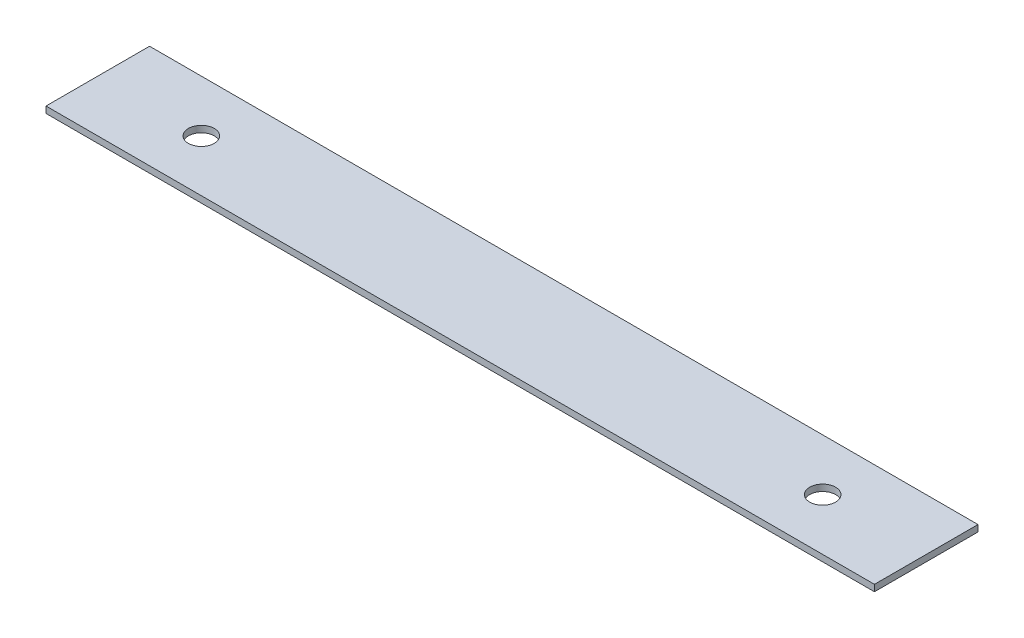
SolidWorks part; units mm, degrees
ref_plane "Front Plane" through (0, 0, 0) normal (0, 0, 1) x (1, 0, 0)
ref_plane "Top Plane" through (0, 0, 0) normal (0, 1, 0) x (1, 0, 0)
ref_plane "Right Plane" through (0, 0, 0) normal (1, 0, 0) x (0, 0, -1)
sketch "Sketch1" plane through (0, 0, 0) normal (0, 1, 0) x (1, 0, 0)
  line L0 (-203.2, 0) -> (203.2, 0) construction
  line L1 (203.2, -25.4) -> (-203.2, -25.4)
  line L2 (203.2, -25.4) -> (203.2, 25.4)
  line L3 (203.2, 25.4) -> (-203.2, 25.4)
  line L4 (-203.2, -25.4) -> (-203.2, 25.4)
  line L5 (203.2, -25.4) -> (-203.2, 25.4) construction
  line L6 (203.2, 25.4) -> (-203.2, -25.4) construction
  line L8 (-209.8879, 25.4) -> (-203.2, 25.4)
  line L10 (209.8879, 25.4) -> (203.2, 25.4)
  circle A0 centre (-152.4, 0) radius 6.35
  circle A1 centre (152.4, 0) radius 6.35
  point P0 (0, 0)
  dimension "D1" = 406.4
  dimension "D5" = 12.7
  dimension "D2" = 50.8
  dimension "D3" = 304.8
  dimension "D4" = 152.4
extrude "Boss-Extrude1" add sketch "Sketch1" along normal blind 3.175
